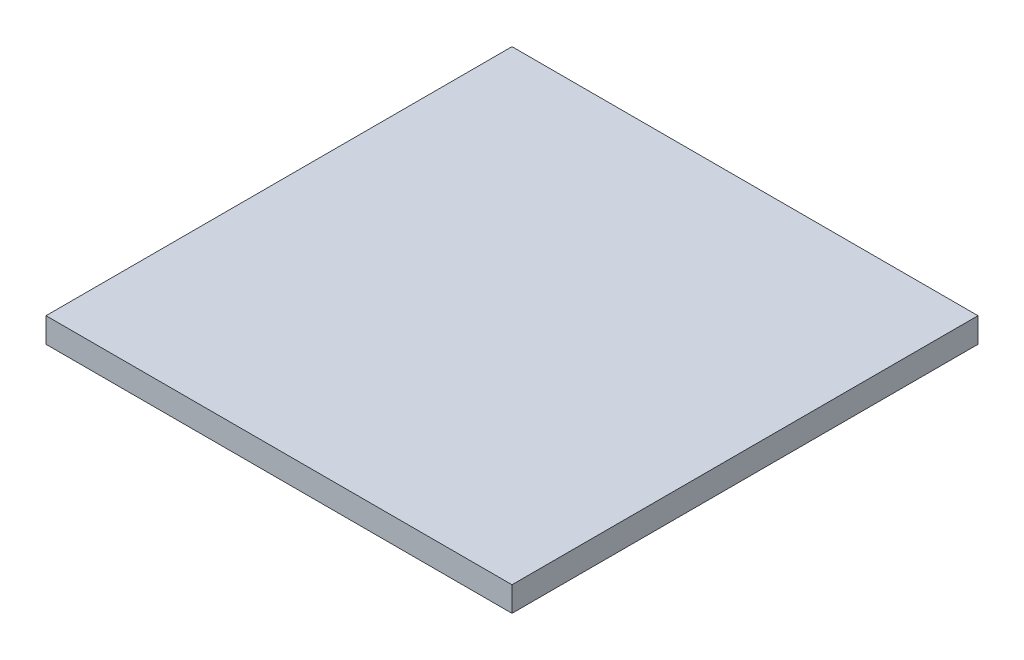
SolidWorks part; units mm, degrees
ref_plane "Front Plane" through (0, 0, 0) normal (0, 0, 1) x (1, 0, 0)
ref_plane "Top Plane" through (0, 0, 0) normal (0, 1, 0) x (1, 0, 0)
ref_plane "Right Plane" through (0, 0, 0) normal (1, 0, 0) x (0, 0, -1)
sketch "Sketch1" plane through (0, 0, 0) normal (0, 1, 0) x (1, 0, 0)
  line L1 (18.6869, 25.3531) -> (-43.3131, 25.3531)
  line L2 (18.6869, 25.3531) -> (18.6869, -36.6469)
  line L3 (18.6869, -36.6469) -> (-43.3131, -36.6469)
  line L4 (-43.3131, 25.3531) -> (-43.3131, -36.6469)
  dimension "D1" = 62
  dimension "D2" = 62
extrude "Boss-Extrude1" add sketch "Sketch1" along normal blind 3.3
